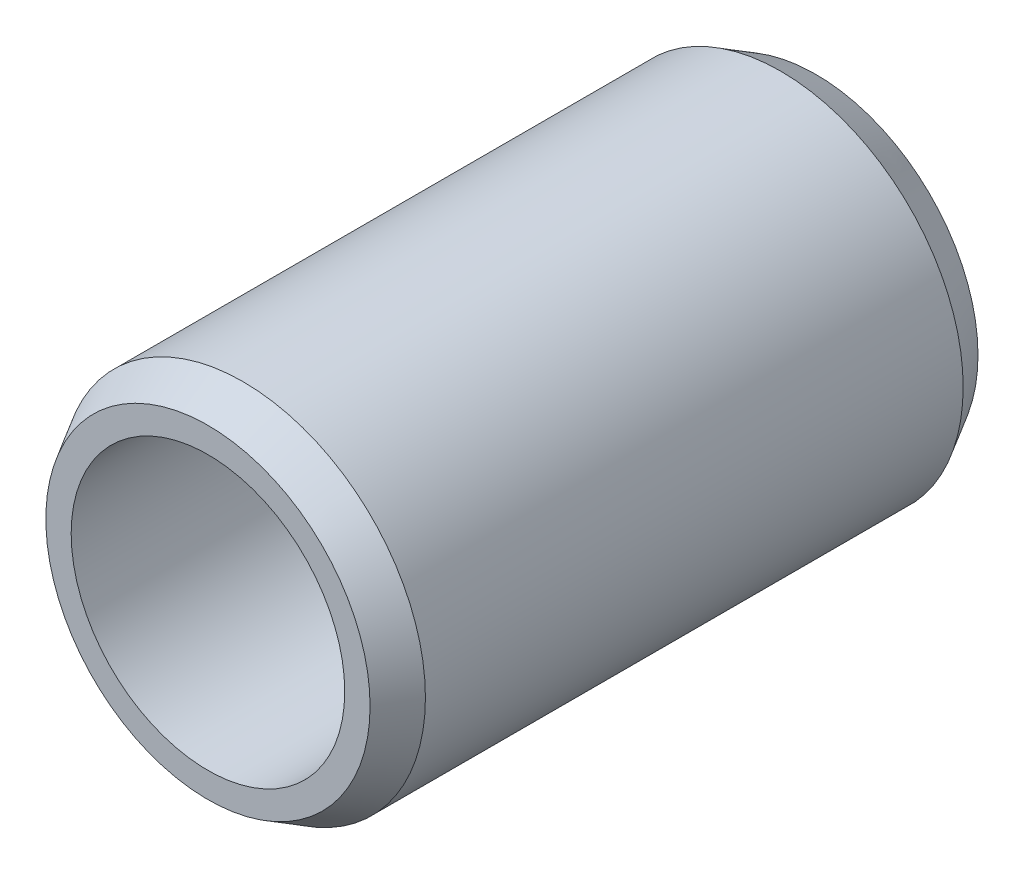
SolidWorks part; units mm, degrees
material "Plain Carbon Steel"
ref_plane "Front Plane" through (0, 0, 0) normal (0, 0, 1) x (1, 0, 0)
ref_plane "Top Plane" through (0, 0, 0) normal (0, 1, 0) x (1, 0, 0)
ref_plane "Right Plane" through (0, 0, 0) normal (1, 0, 0) x (0, 0, -1)
sketch "Sketch1" plane through (0, 0, 0) normal (0, 0, 1) x (1, 0, 0)
  circle A0 centre (0, 0) radius 4.5
  circle A1 centre (0, 0) radius 3.375
  dimension "D1" = 6.75
  dimension "D2" = 9
extrude "Boss-Extrude1" add sketch "Sketch1" along normal blind 15
chamfer "Chamfer1" distance 0.5 angle 60 2 edges at (4.5, 0, 15) (4.5, 0, 0)
